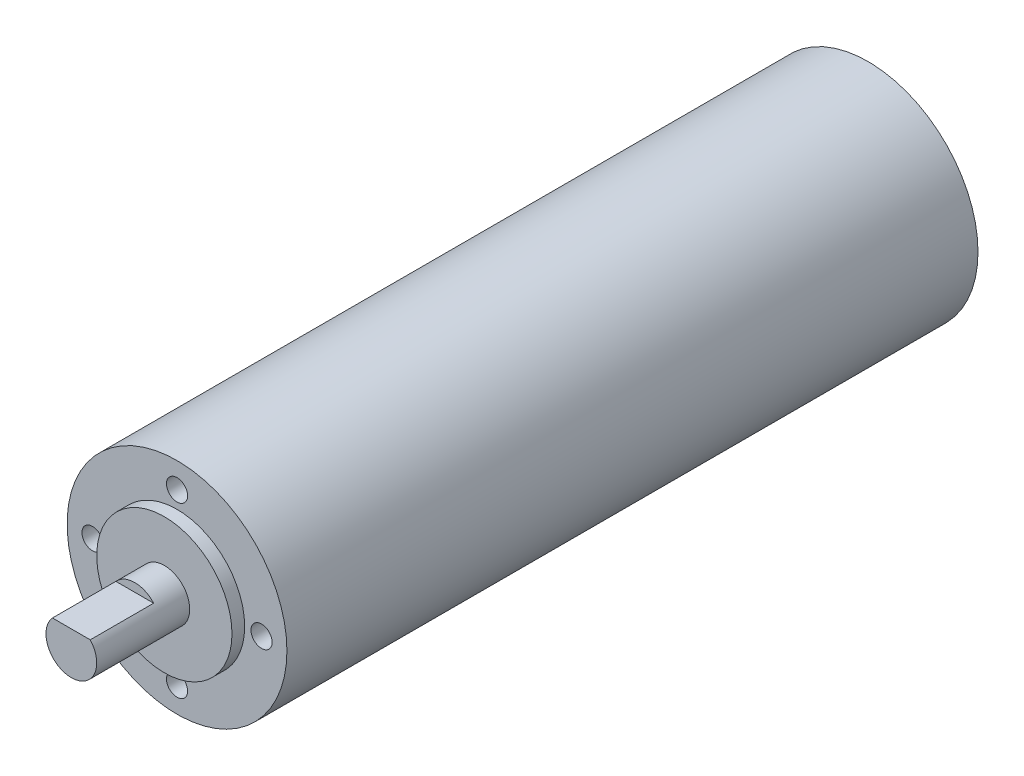
SolidWorks part; units mm, degrees
ref_plane "Front Plane" through (0, 0, 0) normal (0, 0, 1) x (1, 0, 0)
ref_plane "Top Plane" through (0, 0, 0) normal (0, 1, 0) x (1, 0, 0)
ref_plane "Right Plane" through (0, 0, 0) normal (1, 0, 0) x (0, 0, -1)
sketch "Sketch1" plane through (0, 0, 0) normal (0, 0, 1) x (1, 0, 0)
  circle A0 centre (0, 0) radius 26
  dimension "D1" = 52
extrude "Boss-Extrude1" add sketch "Sketch1" along normal blind 163.5
sketch "Sketch2" plane through (0, 0, 163.5) normal (0, 0, 1) x (1, 0, 0)
  circle A0 centre (0, 0) radius 16
  dimension "D1" = 32
extrude "Boss-Extrude2" add sketch "Sketch2" along normal blind 3
sketch "Sketch3" plane through (0, 0, 166.5) normal (0, 0, 1) x (1, 0, 0)
  circle A0 centre (0, 0) radius 6
  dimension "D1" = 12
extrude "Boss-Extrude3" add sketch "Sketch3" along normal blind 22
sketch "Sketch4" plane through (0, 0, 188.5) normal (0, 0, 1) x (1, 0, 0)
  line L0 (0, -6) -> (0, 4) construction
  line L1 (-5.4556, 4) -> (-5.4556, 6.3056)
  line L2 (-5.4556, 4) -> (5.4556, 4)
  line L3 (0, 4) -> (0, 6.3056)
  line L4 (-5.4556, 6.3056) -> (5.4556, 6.3056)
  line L5 (5.4556, 4) -> (5.4556, 6.3056)
  circle A0 centre (0, 0) radius 6 construction
  circle A1 centre (0, 0) radius 6 construction
  circle M1 centre (0, 0) radius 6
  dimension "D1" = 10
extrude "Cut-Extrude1" cut sketch "Sketch4" against normal blind 15 contours L2 L3 M1 | L3 L2 M1
sketch "Sketch6" plane through (0, 0, 163.5) normal (0, 0, 1) x (1, 0, 0)
  line L0 (0, 0) -> (0, 26) construction
  circle A0 centre (0, 0) radius 26 construction
  circle A1 centre (0, 20) radius 2.5
  circle A2 centre (20, 0) radius 2.5
  circle A3 centre (0, -20) radius 2.5
  circle A4 centre (-20, 0) radius 2.5
  point P17 (0, 0)
  dimension "D2" = 5
  dimension "D1" = 20
  dimension "D3" = 4
extrude "Cut-Extrude2" cut sketch "Sketch6" against normal blind 10
